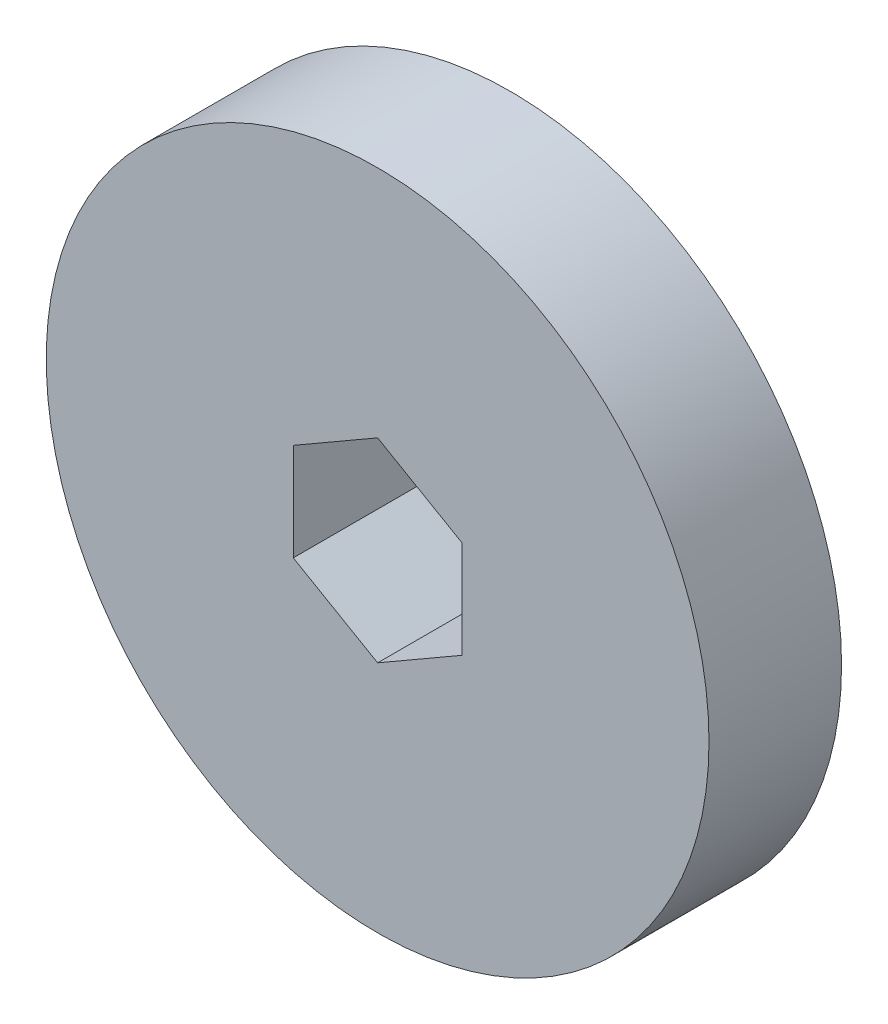
SolidWorks part; units mm, degrees
ref_plane "Front Plane" through (0, 0, 0) normal (0, 0, 1) x (1, 0, 0)
ref_plane "Top Plane" through (0, 0, 0) normal (0, 1, 0) x (1, 0, 0)
ref_plane "Right Plane" through (0, 0, 0) normal (1, 0, 0) x (0, 0, -1)
sketch "Sketch1" plane through (0, 0, 0) normal (0, 0, 1) x (1, 0, 0)
  circle A0 centre (0, 0) radius 25
  dimension "D1" = 50
extrude "Boss-Extrude2" add sketch "Sketch1" along normal blind 10
sketch "Sketch2" plane through (0, 0, 10) normal (0, 0, 1) x (1, 0, 0)
  line L1 (0, 7.3497) -> (-6.365, 3.6748)
  line L2 (-6.365, 3.6748) -> (-6.365, -3.6748)
  line L3 (-6.365, -3.6748) -> (0, -7.3497)
  line L4 (0, -7.3497) -> (6.365, -3.6748)
  line L5 (6.365, -3.6748) -> (6.365, 3.6748)
  line L6 (6.365, 3.6748) -> (0, 7.3497)
  circle A0 centre (0, 0) radius 6.365 construction
extrude "Cut-Extrude1" cut sketch "Sketch2" against normal blind 10
